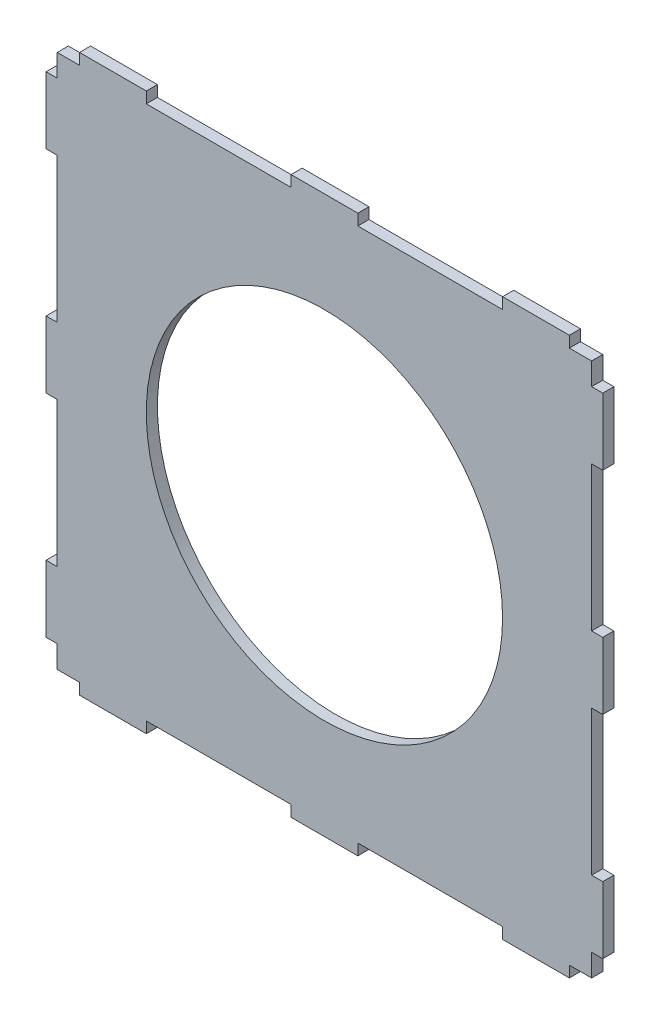
SolidWorks part; units mm, degrees
ref_plane "Front Plane" through (0, 0, 0) normal (0, 0, 1) x (1, 0, 0)
ref_plane "Top Plane" through (0, 0, 0) normal (0, 1, 0) x (1, 0, 0)
ref_plane "Right Plane" through (0, 0, 0) normal (1, 0, 0) x (0, 0, -1)
sketch "Sketch1" plane through (0, 0, 0) normal (0, 0, 1) x (1, 0, 0)
  line L1 (-120, 120) -> (120, 120)
  line L2 (-120, 120) -> (-120, -120)
  line L3 (-120, -120) -> (120, -120)
  line L4 (120, 120) -> (120, -120)
  line L5 (-120, 120) -> (120, -120) construction
  line L6 (-120, -120) -> (120, 120) construction
  line L7 (-110, 120) -> (-80, 120)
  line L8 (-110, 120) -> (-110, 125)
  line L9 (-110, 125) -> (-80, 125)
  line L10 (-80, 120) -> (-80, 125)
  line L11 (-15, 120) -> (15, 120)
  line L12 (-15, 120) -> (-15, 125)
  line L13 (-15, 125) -> (15, 125)
  line L14 (15, 120) -> (15, 125)
  line L15 (80, 120) -> (110, 120)
  line L16 (80, 120) -> (80, 125)
  line L17 (80, 125) -> (110, 125)
  line L18 (110, 120) -> (110, 125)
  line L19 (120, 110) -> (125, 110)
  line L20 (120, 110) -> (120, 80)
  line L21 (120, 80) -> (125, 80)
  line L22 (125, 110) -> (125, 80)
  line L23 (120, 15) -> (125, 15)
  line L24 (120, 15) -> (120, -15)
  line L25 (120, -15) -> (125, -15)
  line L26 (125, 15) -> (125, -15)
  line L27 (120, -80) -> (125, -80)
  line L28 (120, -80) -> (120, -110)
  line L29 (120, -110) -> (125, -110)
  line L30 (125, -80) -> (125, -110)
  line L31 (110, -120) -> (80, -120)
  line L32 (110, -120) -> (110, -125)
  line L33 (110, -125) -> (80, -125)
  line L34 (80, -120) -> (80, -125)
  line L35 (15, -120) -> (-15, -120)
  line L36 (15, -120) -> (15, -125)
  line L37 (15, -125) -> (-15, -125)
  line L38 (-15, -120) -> (-15, -125)
  line L39 (-80, -120) -> (-110, -120)
  line L40 (-80, -120) -> (-80, -125)
  line L41 (-80, -125) -> (-110, -125)
  line L42 (-110, -120) -> (-110, -125)
  line L43 (-120, -110) -> (-125, -110)
  line L44 (-120, -110) -> (-120, -80)
  line L45 (-120, -80) -> (-125, -80)
  line L46 (-125, -110) -> (-125, -80)
  line L47 (-120, -15) -> (-125, -15)
  line L48 (-120, -15) -> (-120, 15)
  line L49 (-120, 15) -> (-125, 15)
  line L50 (-125, -15) -> (-125, 15)
  line L51 (-120, 80) -> (-125, 80)
  line L52 (-120, 80) -> (-120, 110)
  line L53 (-120, 110) -> (-125, 110)
  line L54 (-125, 80) -> (-125, 110)
  circle A0 centre (0, 0) radius 80
  point P0 (0, 0)
  dimension "D3" = 160
  dimension "D1" = 240
  dimension "D2" = 240
  dimension "D4" = 30
  dimension "D5" = 5
  dimension "D6" = 10
  dimension "D7" = 65
  dimension "D8" = 30
  dimension "D9" = 5
  dimension "D10" = 65
  dimension "D11" = 30
  dimension "D12" = 5
  dimension "D13" = 5
  dimension "D14" = 30
  dimension "D15" = 30
  dimension "D16" = 30
  dimension "D17" = 5
  dimension "D18" = 5
  dimension "D19" = 65
  dimension "D20" = 10
  dimension "D21" = 65
  dimension "D22" = 30
  dimension "D23" = 5
  dimension "D24" = 5
  dimension "D25" = 5
  dimension "D26" = 30
  dimension "D27" = 30
  dimension "D28" = 10
  dimension "D29" = 65
  dimension "D30" = 65
  dimension "D31" = 30
  dimension "D32" = 30
  dimension "D33" = 30
  dimension "D34" = 5
  dimension "D35" = 5
  dimension "D36" = 5
  dimension "D37" = 10
  dimension "D38" = 65
  dimension "D39" = 65
extrude "Boss-Extrude1" add sketch "Sketch1" along normal blind 5 contours L4 L1 L2 L3 A0 | L54 L51 L2 L53 | L1 L10 L9 L8 | L1 L14 L13 L12 | L1 L18 L17 L16 | L22 L19 L4 L21 | L26 L23 L4 L25 | L30 L27 L4 L29 | L3 L34 L33 L32 | L3 L38 L37 L36 | L46 L43 L2 L45 | L50 L47 L2 L49 | L41 L42 L39 L40
